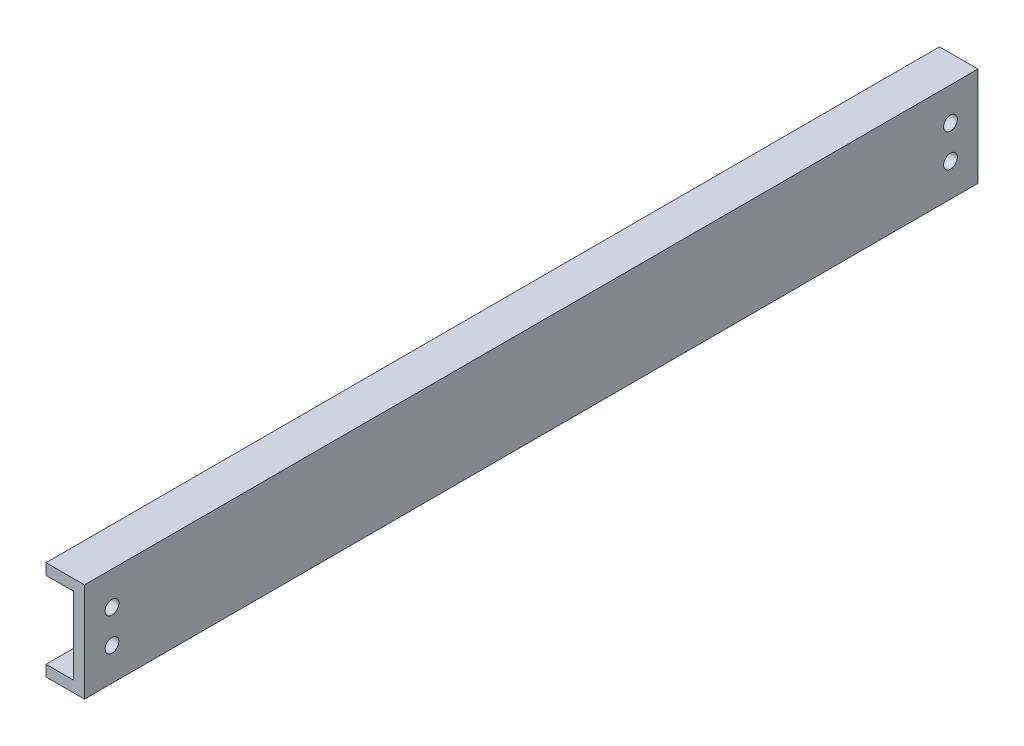
SolidWorks part; units mm, degrees
ref_plane "Front Plane" through (0, 0, 0) normal (0, 0, 1) x (1, 0, 0)
ref_plane "Top Plane" through (0, 0, 0) normal (0, 1, 0) x (1, 0, 0)
ref_plane "Right Plane" through (0, 0, 0) normal (1, 0, 0) x (0, 0, -1)
sketch "Sketch1" plane through (0, 0, 0) normal (0, 0, 1) x (1, 0, 0)
  line L0 (-7, 9.8883) -> (0, 9.8883)
  line L1 (0, 9.8883) -> (0, -8.1117)
  line L2 (0, -8.1117) -> (-7, -8.1117)
  line L3 (-7, 7.8883) -> (-2, 7.8883)
  line L4 (-2, 7.8883) -> (-2, -6.1117)
  line L5 (-2, -6.1117) -> (-7, -6.1117)
  line L6 (-7, 9.8883) -> (-7, 7.8883)
  line L7 (-7, -8.1117) -> (-7, -6.1117)
  dimension "D1" = 18
  dimension "D2" = 7
  dimension "D3" = 7
  dimension "D4" = 2
extrude "Boss-Extrude1" add sketch "Sketch1" against normal blind 162.5
sketch "Sketch2" plane through (0, 0, 0) normal (1, 0, 0) x (0, 0, -1)
  line L0 (0, 0.8883) -> (162.5, 0.8883) construction
  line L3 (0, -8.1117) -> (0, 9.8883) construction
  line L4 (162.5, -8.1117) -> (162.5, 9.8883) construction
  line L5 (162.5, -8.1117) -> (0, -8.1117) construction
  line L6 (2, 9.8883) -> (2, -8.1117) construction
  line L7 (162.5, 9.8883) -> (0, 9.8883) construction
  line L8 (81.25, 9.8883) -> (81.25, -8.1117) construction
  circle A0 centre (5, 3.8883) radius 1.25
  circle A2 centre (5, -2.1117) radius 1.25
  circle A3 centre (157.5, -2.1117) radius 1.25
  circle A4 centre (157.5, 3.8883) radius 1.25
  dimension "D2" = 2.5
  dimension "D1" = 2
  dimension "D3" = 3
  dimension "D4" = 3
extrude "Cut-Extrude1" cut sketch "Sketch2" against normal through all
